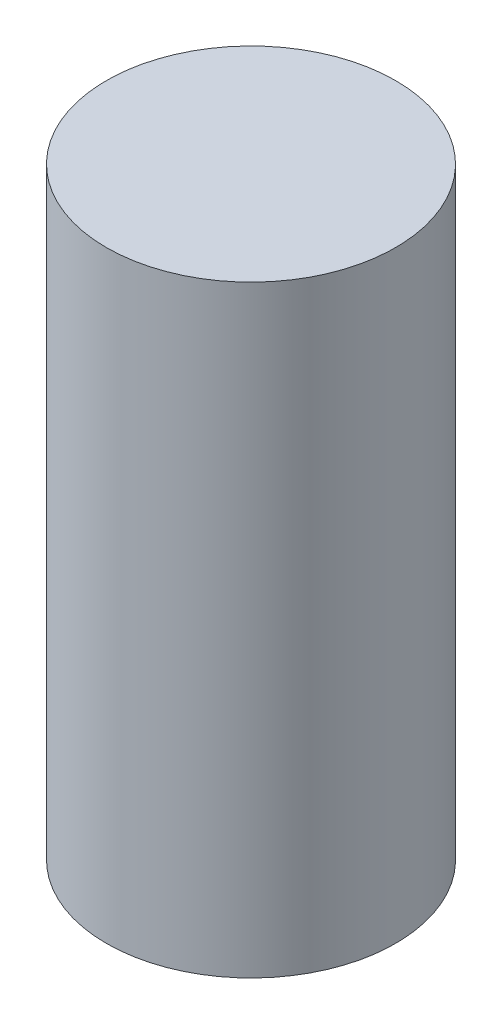
SolidWorks part; units mm, degrees
ref_plane "Front Plane" through (0, 0, 0) normal (0, 0, 1) x (1, 0, 0)
ref_plane "Top Plane" through (0, 0, 0) normal (0, 1, 0) x (1, 0, 0)
ref_plane "Right Plane" through (0, 0, 0) normal (1, 0, 0) x (0, 0, -1)
sketch "Sketch1" plane through (0, 0, 0) normal (0, 1, 0) x (1, 0, 0)
  circle A0 centre (0, 0) radius 1.92
  dimension "D1" = 3.84
extrude "Boss-Extrude1" add sketch "Sketch1" along normal blind 8
